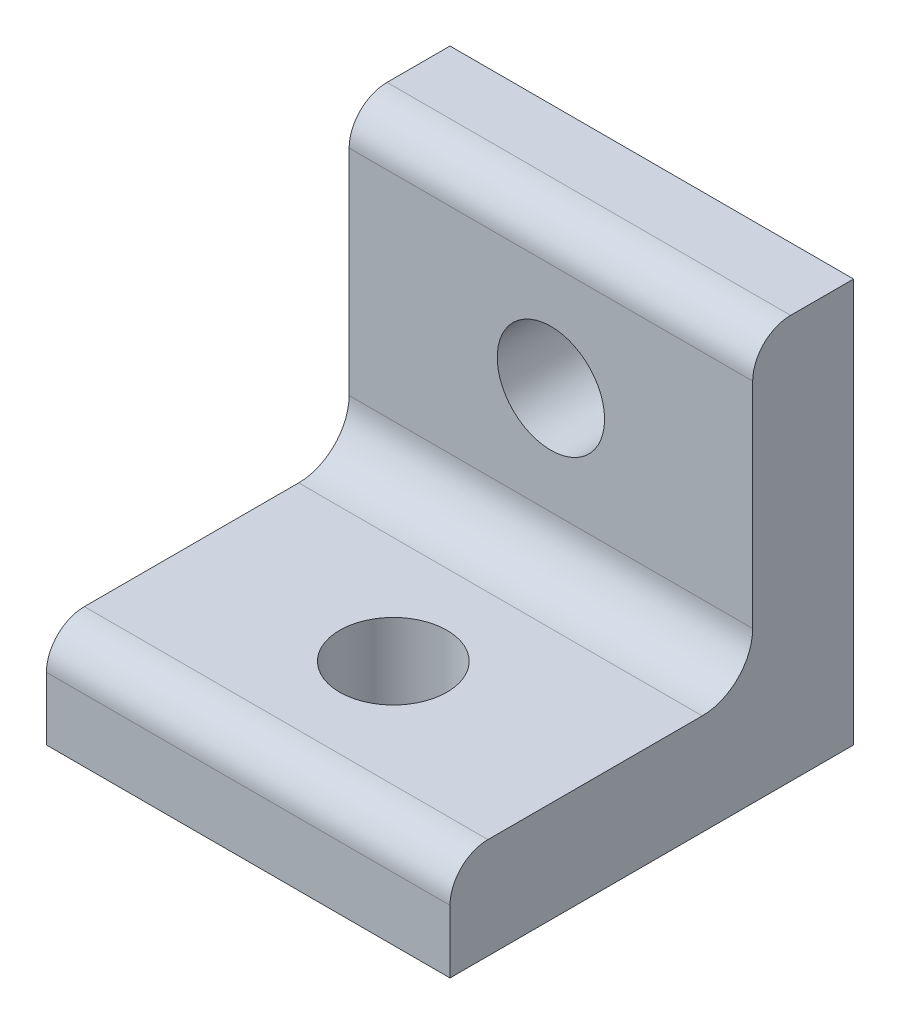
SolidWorks part; units mm, degrees
ref_plane "Front Plane" through (0, 0, 0) normal (0, 0, 1) x (1, 0, 0)
ref_plane "Top Plane" through (0, 0, 0) normal (0, 1, 0) x (1, 0, 0)
ref_plane "Right Plane" through (0, 0, 0) normal (1, 0, 0) x (0, 0, -1)
sketch "Sketch1" plane through (0, 0, 0) normal (0, 1, 0) x (1, 0, 0)
  line L1 (0, 0) -> (25.4, 0)
  line L2 (0, 0) -> (0, 25.4)
  line L3 (0, 25.4) -> (25.4, 25.4)
  line L4 (25.4, 0) -> (25.4, 25.4)
  dimension "D1" = 25.4
  dimension "D2" = 25.4
extrude "Boss-Extrude1" add sketch "Sketch1" along normal blind 6.35
sketch "Sketch2" plane through (0, 0, -25.4) normal (0, 0, -1) x (-1, 0, 0)
  line L1 (0, 0) -> (-25.4, 0)
  line L2 (0, 0) -> (0, 25.4)
  line L3 (0, 25.4) -> (-25.4, 25.4)
  line L4 (-25.4, 0) -> (-25.4, 25.4)
  dimension "D1" = 25.4
  dimension "D2" = 25.4
extrude "Boss-Extrude2" add sketch "Sketch2" against normal blind 6.35
fillet "Fillet1" radius 3.175 1 edges at (12.7, 6.35, -19.05)
fillet "Fillet2" radius 2.3876 2 edges at (12.7, 6.35, 0) (12.7, 25.4, -19.05)
sketch "Sketch3" plane through (0, 6.35, 0) normal (0, 1, 0) x (1, 0, 0)
  line L0 (25.4, 15.875) -> (0, 15.875) construction
  line L2 (0, 15.875) -> (0, 2.3876) construction
  line L3 (25.4, 2.3876) -> (25.4, 15.875) construction
  circle A0 centre (12.7, 9.1313) radius 3.3782
  circle A1 centre (29.8044, 9.1313) radius 3.3782
  circle A2 centre (46.3956, 9.1313) radius 3.3782
  circle A3 centre (33.5001, 19.5704) radius 3.3782
  point P17 (25.4, 9.1313)
  dimension "D1" = 6.7564
  dimension "D2" = 6.7564
  dimension "D3" = 6.7564
  dimension "D4" = 6.7564
  dimension "D5" = 12.7
  dimension "D11" = 6.7437
  dimension "D7" = 16.5913
  dimension "D8" = 16.5913
  dimension "D9" = 13.2131
  dimension "D10" = 6.7437
  dimension "D12" = 6.7437
extrude "Cut-Extrude1" cut sketch "Sketch3" against normal through all
sketch "Sketch4" plane through (0, 0, -19.05) normal (0, 0, 1) x (1, 0, 0)
  line L0 (0, 9.525) -> (25.4, 9.525) construction
  line L2 (25.4, 23.0124) -> (25.4, 9.525) construction
  circle A0 centre (-37.0738, 16.2687) radius 3.3782
  circle A1 centre (-20.4826, 16.2687) radius 3.3782
  circle A2 centre (-3.8913, 16.2687) radius 3.3782
  circle A3 centre (12.7, 16.2687) radius 3.3782
  dimension "D1" = 6.7564
  dimension "D2" = 6.7564
  dimension "D3" = 6.7564
  dimension "D4" = 6.7564
  dimension "D12" = 12.7
  dimension "D5" = 6.7437
  dimension "D6" = 6.7437
  dimension "D7" = 6.7437
  dimension "D8" = 6.7437
  dimension "D9" = 16.5913
  dimension "D10" = 16.5913
  dimension "D11" = 16.5913
extrude "Cut-Extrude2" cut sketch "Sketch4" against normal through all
